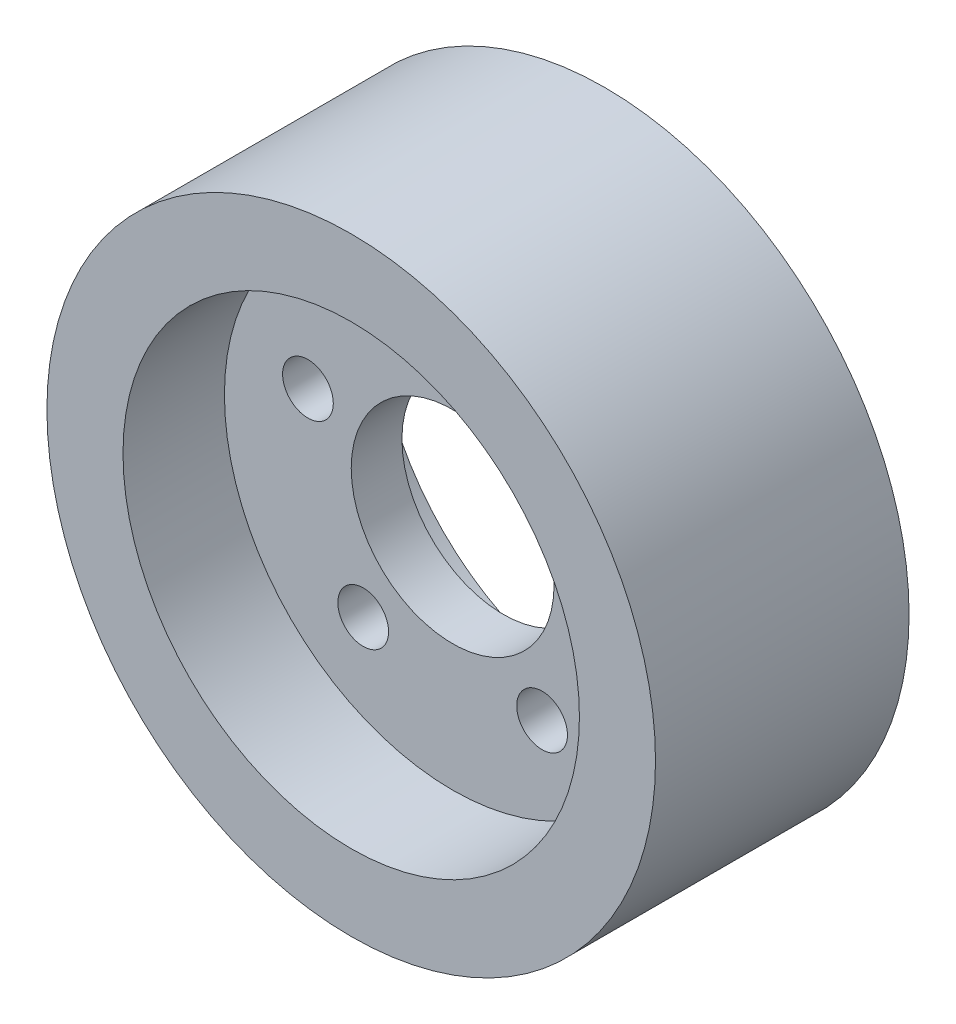
SolidWorks part; units mm, degrees
ref_plane "Front Plane" through (0, 0, 0) normal (0, 0, 1) x (1, 0, 0)
ref_plane "Top Plane" through (0, 0, 0) normal (0, 1, 0) x (1, 0, 0)
ref_plane "Right Plane" through (0, 0, 0) normal (1, 0, 0) x (0, 0, -1)
sketch "Sketch1" plane through (0, 0, 0) normal (0, 0, 1) x (1, 0, 0)
  circle A0 centre (0, 0) radius 10
  circle A1 centre (0, 0) radius 30
  dimension "D1" = 20
  dimension "D2" = 60
extrude "Boss-Extrude1" add sketch "Sketch1" along normal mid plane 25
sketch "Sketch2" plane through (0, 0, -12.5) normal (0, 0, -1) x (-1, 0, 0)
  circle A0 centre (0, 0) radius 22.5
  dimension "D1" = 45
extrude "Cut-Extrude1" cut sketch "Sketch2" against normal blind 10 contours A0
mirror "Mirror1" about plane through (0, 0, 0) normal (0, 0, 1) of "Cut-Extrude1"
sketch "Sketch3" plane through (0, 0, -2.5) normal (0, 0, -1) x (-1, 0, 0)
  circle A0 centre (0, 15) radius 2.5
  dimension "D1" = 5
  dimension "D2" = 15
extrude "Cut-Extrude2" cut sketch "Sketch3" against normal through all
pattern_circular "CirPattern3" count 5 over 360 about axis through (0, 0, 0) along (0, 0, 1) of "Cut-Extrude2"
sketch "Sketch6" plane through (0, 0, 0) normal (0, 1, 0) x (1, 0, 0)
  line L0 (30, 7.5) -> (23.0718, 3.5)
  line L1 (30, -12.5) -> (30, 12.5) construction
  line L2 (23.0718, 3.5) -> (23.0718, -3.5)
  line L3 (23.0718, -3.5) -> (30, -7.5)
  line L4 (30, -7.5) -> (30, 7.5)
  line L5 (30, 12.5) -> (-30, 12.5) construction
  line L6 (-30, -12.5) -> (30, -12.5) construction
  point P8 (0, 0)
  point P13 (37.3746, -7.6294)
  point P14 (38.919, -7.8147)
  dimension "D1" = 120
  dimension "D2" = 5
  dimension "D3" = 5
  dimension "D4" = 60
  dimension "D5" = 7
sketch "Sketch7" plane through (0, 0, 0) normal (0, 1, 0) x (1, 0, 0)
  line L0 (0, 0) -> (0, 20.1699) construction
  line L1 (23.0718, -3.5) -> (30, -7.5) construction
  line L2 (23.0718, 3.5) -> (23.0718, -3.5) construction
  line L3 (30, -7.5) -> (30, 7.5) construction
pattern_circular "CirPattern2" count 5 over 360
sketch "Sketch5" plane through (0, 0, 0) normal (0, 1, 0) x (1, 0, 0)
  line L0 (0, 0) -> (0, 20.2405) construction
  line L1 (30, 7.5) -> (24, 4.0359)
  line L2 (30, -12.5) -> (30, 12.5) construction
  line L3 (24, -3.9641) -> (24, 4.0359)
  line L4 (24, 4.0359) -> (24, -3.9641)
  line L5 (24, -3.9641) -> (30, -7.4282)
  line L7 (30, -7.4282) -> (30, 7.5)
  line L8 (30, 12.5) -> (-30, 12.5) construction
  dimension "D1" = 8
  dimension "D2" = 120
  dimension "D3" = 120
  dimension "D4" = 6
  dimension "D5" = 5
